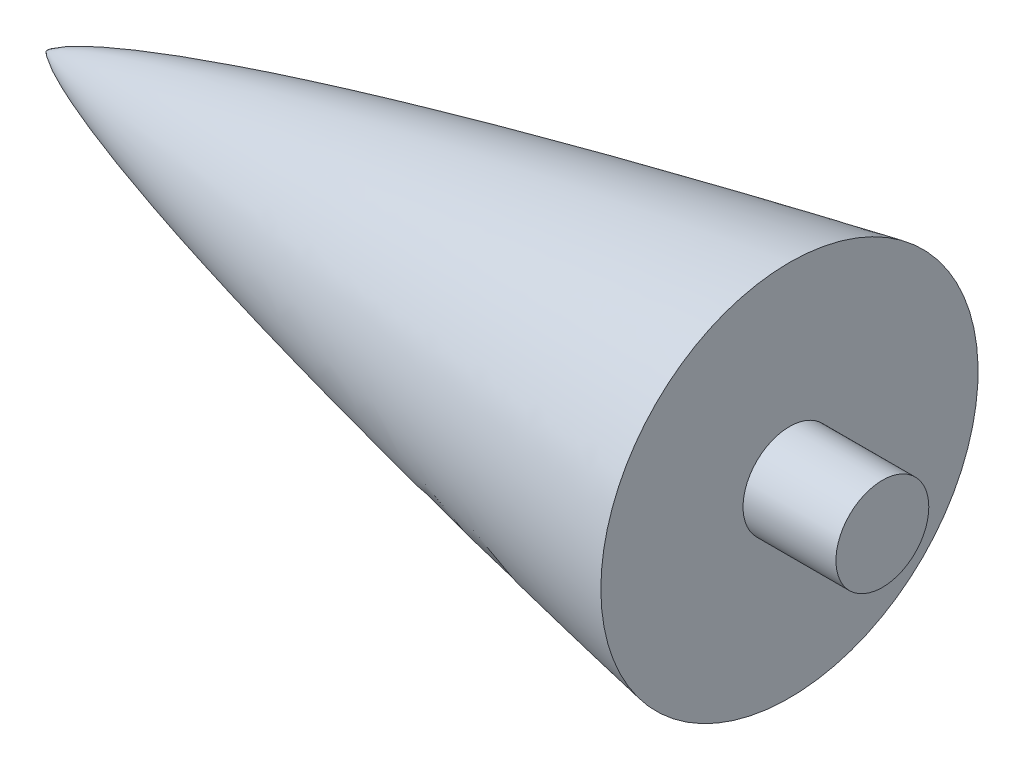
SolidWorks part; units mm, degrees
material "AISI 304"
ref_plane "Front Plane" through (0, 0, 0) normal (0, 0, 1) x (1, 0, 0)
ref_plane "Top Plane" through (0, 0, 0) normal (0, 1, 0) x (1, 0, 0)
ref_plane "Right Plane" through (0, 0, 0) normal (1, 0, 0) x (0, 0, -1)
sketch "Sketch3" plane through (0, 0, 0) normal (0, 0, 1) x (1, 0, 0)
  line L0 (0, 0) -> (101.6, 0)
  line L1 (101.6, 0) -> (101.6, 25.7872)
  line L2 (101.6, 0) -> (183.1013, 0) construction
  line L3 (183.1013, 0) -> (241.0357, 0) construction
  spline S0 degree 4 poles (0, 0) (0.0024, 0.0076) (0.008, 0.0224) (0.0228, 0.0502) (0.0602, 0.1013) (0.1177, 0.1662) (0.1973, 0.2429) (0.3166, 0.346) (0.4663, 0.4619) (0.6411, 0.5854) (0.8409, 0.7163) (1.0863, 0.8681) (1.3805, 1.0392) (1.7304, 1.2306) (2.1039, 1.4235) (2.4495, 1.5946) (2.8343, 1.779) (3.3252, 2.0064) (3.9582, 2.287) (5.2484, 2.832) (7.7002, 3.7871) (12.4184, 5.4349) (21.4879, 8.2045) (34.2024, 11.5666) (49.9837, 15.3041) (77.2138, 21.1912) (111.5094, 27.7893) (153.1274, 35.0456) (202.0796, 42.8366) (248.6768, 49.7602) (306.9942, 57.9227) (377.0645, 67.0588) (458.9113, 76.9376) (552.5524, 87.3436) (646.2759, 96.9776) (740.0687, 105.9093) (833.9221, 114.1801) (927.8297, 121.8101) (1021.7871, 128.8013) (1115.791, 135.1367) (1198.0833, 140.0715) (1268.6466, 143.8211) (1327.4672, 146.5841) (1374.5344, 148.5535) (1414.7685, 150.0006) (1448.1647, 151.0109) (1474.7196, 151.6715) (1491.9662, 152.0244) (1506.7504, 152.259) (1516.6071, 152.3627) (1521.5357, 152.3956) (1524, 152.4) knots 0 0 0 0 0 0.000021 0.000041 0.000082 0.000164 0.000247 0.000329 0.000493 0.000658 0.000805 0.000951 0.001245 0.001545 0.001844 0.002047 0.002251 0.002657 0.003255 0.003853 0.005902 0.009516 0.016281 0.028569 0.040181 0.051794 0.088907 0.119611 0.150314 0.181018 0.211721 0.273128 0.334535 0.395942 0.457348 0.518755 0.580162 0.641569 0.702976 0.764383 0.825789 0.856493 0.887196 0.9179 0.948603 0.961452 0.974302 0.987151 0.993575 1 1 1 1 1 construction
  spline S1 degree 4 poles (0, 0) (0.0024, 0.0076) (0.008, 0.0224) (0.0228, 0.0502) (0.0602, 0.1013) (0.1177, 0.1662) (0.1973, 0.2429) (0.3166, 0.346) (0.4663, 0.4619) (0.6411, 0.5854) (0.8409, 0.7163) (1.0863, 0.8681) (1.3805, 1.0392) (1.7304, 1.2306) (2.1039, 1.4235) (2.4495, 1.5946) (2.8343, 1.779) (3.3252, 2.0064) (3.9582, 2.287) (5.2484, 2.832) (7.7002, 3.7871) (12.4184, 5.4349) (21.4879, 8.2045) (34.2024, 11.5666) (49.9837, 15.3041) (77.2138, 21.1912) (111.5094, 27.7893) (153.1274, 35.0456) (202.0796, 42.8366) (248.6768, 49.7602) (306.9942, 57.9227) (377.0645, 67.0588) (458.9113, 76.9376) (552.5524, 87.3436) (646.2759, 96.9776) (740.0687, 105.9093) (833.9221, 114.1801) (927.8297, 121.8101) (1021.7871, 128.8013) (1115.791, 135.1367) (1198.0833, 140.0715) (1268.6466, 143.8211) (1327.4672, 146.5841) (1374.5344, 148.5535) (1414.7685, 150.0006) (1448.1647, 151.0109) (1474.7196, 151.6715) (1491.9662, 152.0244) (1506.7504, 152.259) (1516.6071, 152.3627) (1521.5357, 152.3956) (1524, 152.4) knots 0 0 0 0 0 0.000021 0.000041 0.000082 0.000164 0.000247 0.000329 0.000493 0.000658 0.000805 0.000951 0.001245 0.001545 0.001844 0.002047 0.002251 0.002657 0.003255 0.003853 0.005902 0.009516 0.016281 0.028569 0.040181 0.051794 0.088907 0.119611 0.150314 0.181018 0.211721 0.273128 0.334535 0.395942 0.457348 0.518755 0.580162 0.641569 0.702976 0.764383 0.825789 0.856493 0.887196 0.9179 0.948603 0.961452 0.974302 0.987151 0.993575 1 1 1 1 1
  dimension "D1" = 152.4
  dimension "D2" = 101.6
revolve "Revolve1" add sketch "Sketch3" angle 360 about L3
sketch "Sketch4" plane through (101.6, 0, 0) normal (1, 0, 0) x (0, 0, -1)
  circle A0 centre (0, 0) radius 6.35
  dimension "D1" = 12.7
extrude "Boss-Extrude1" add sketch "Sketch4" along normal blind 12.7
equation "\"R\"= 6in"
equation "\"Fineness\"= 5"
equation "\"L\"= 2 * \"R\" * \"Fineness\""
equation "\"Thick\"= 0.125in"
equation "\"D3@Sketch1\"= \"Thick\""
equation "\"Airframe Thickness\"= .25in"
equation "\"D4@Sketch1\"=\"Airframe Thickness\""
equation "\"D7@Sketch1\"=\"R\""
equation "\"D6@Sketch1\"=\"Thick\""
equation "\"D9@Sketch1\"=\"L\"+6in"
equation "\"D1@Sketch3\"=\"R\""
